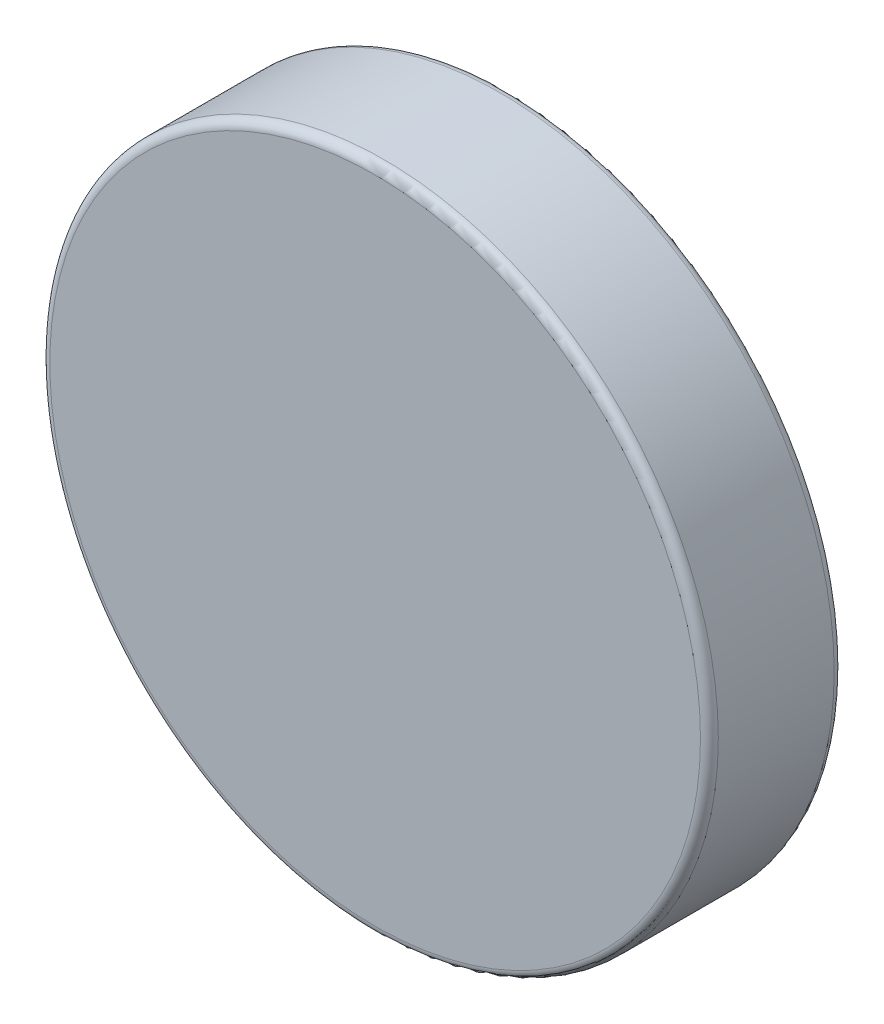
SolidWorks part; units mm, degrees
ref_plane "前视基准面" through (0, 0, 0) normal (0, 0, 1) x (1, 0, 0)
ref_plane "上视基准面" through (0, 0, 0) normal (0, 1, 0) x (1, 0, 0)
ref_plane "右视基准面" through (0, 0, 0) normal (1, 0, 0) x (0, 0, -1)
sketch "草图1" plane through (0, 0, 0) normal (0, 0, 1) x (1, 0, 0)
  circle A0 centre (0, 0) radius 7.5
  dimension "D1" = 15
extrude "凸台-拉伸1" add sketch "草图1" along normal blind 3
fillet "圆角1" radius 0.2 2 edges at (7.5, 0, 0) (7.5, 0, 3)
